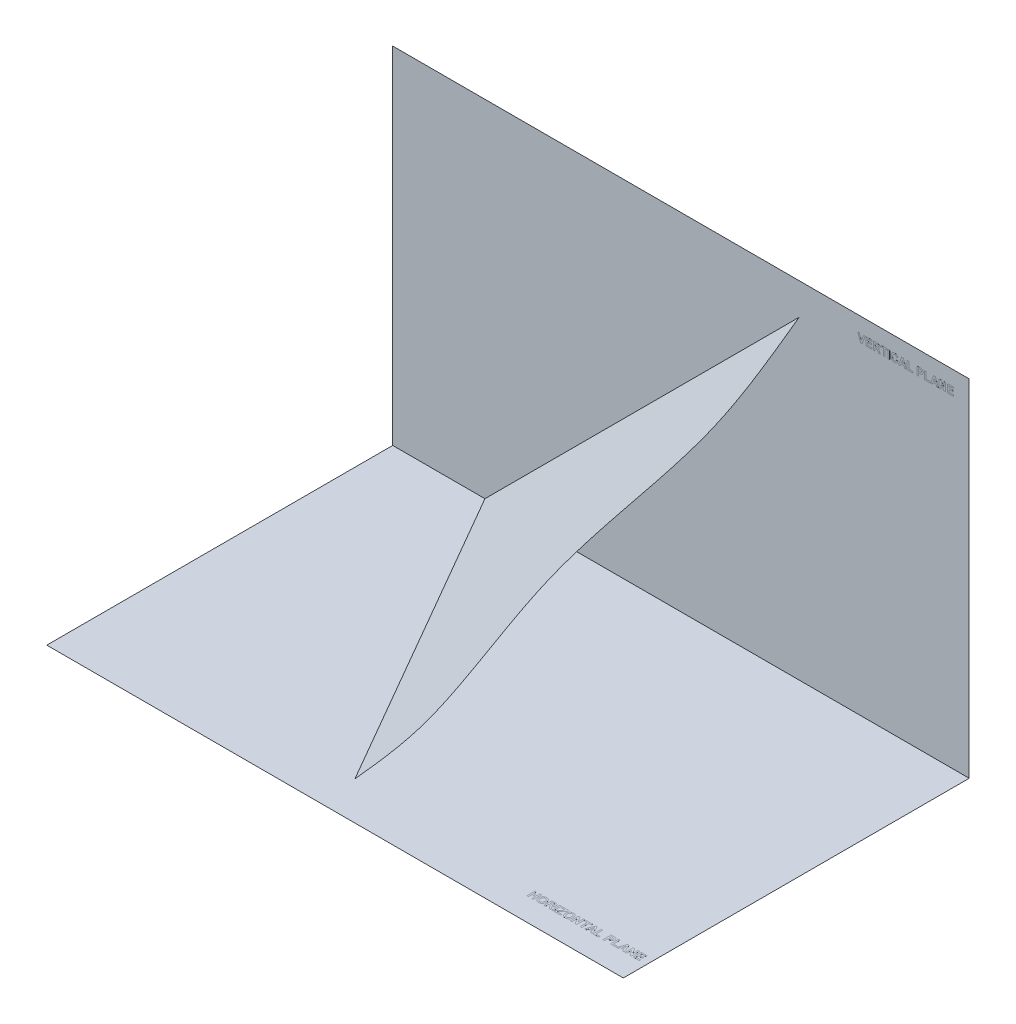
SolidWorks part; units mm, degrees
ref_plane "Front Plane" through (0, 0, 0) normal (0, 0, 1) x (1, 0, 0)
ref_plane "Top Plane" through (0, 0, 0) normal (0, 1, 0) x (1, 0, 0)
ref_plane "Right Plane" through (0, 0, 0) normal (1, 0, 0) x (0, 0, -1)
sketch "Sketch1" plane through (0, 0, 0) normal (0, 0, 1) x (1, 0, 0)
  line L1 (-40, 0) -> (210, 0)
  line L2 (-40, 0) -> (-40, 150)
  line L3 (-40, 150) -> (210, 150)
  line L4 (210, 0) -> (210, 150)
  dimension "D1" = 250
  dimension "D2" = 150
  dimension "D3" = 40
surface "Vertical Plane" sketch "Sketch1"
sketch "Sketch6" plane through (0, 0, 0) normal (0, 0, 1) x (1, 0, 0)
  line L0 (155, 140) -> (210, 140) construction
  line L1 (210, 0) -> (210, 150) construction
  line L2 (210, 150) -> (-40, 150) construction
  text T0 "VERTICAL PLANE" font "Arial" height 3.5
  dimension "D1" = 10
  dimension "D2" = 55
extrude "Vertical  Plane text" add sketch "Sketch6" along normal blind 0.01
sketch "Sketch2" plane through (0, 0, 0) normal (0, 1, 0) x (1, 0, 0)
  line L1 (-40, 0) -> (210, 0)
  line L2 (-40, 0) -> (-40, -150)
  line L3 (-40, -150) -> (210, -150)
  line L4 (210, 0) -> (210, -150)
  dimension "D2" = 150
surface "Horizontal Plane" sketch "Sketch2"
sketch "Sketch7" plane through (0, 0, 0) normal (0, 1, 0) x (1, 0, 0)
  line L0 (155, -140) -> (210, -140) construction
  line L1 (210, -150) -> (210, 0) construction
  line L2 (-40, -150) -> (210, -150) construction
  text T0 "HORIZONTAL PLANE" font "Arial" height 3.5
  dimension "D1" = 10
  dimension "D2" = 55
extrude "Horizontal Plane text" add sketch "Sketch7" along normal blind 0.01
sketch "Vertical Trace" plane through (0, 0, 0) normal (0, 0, 1) x (1, 0, 0)
  line L0 (0, 0) -> (136.2234, 136.2234) construction
  line L1 (210, 0) -> (-40, 0) construction
  dimension "D1" = 45
sketch "Horizontal Trace" plane through (0, 0, 0) normal (0, 1, 0) x (1, 0, 0)
  line L0 (0, 0) -> (77.0291, -133.4183) construction
  line L1 (210, 0) -> (-40, 0) construction
  dimension "D1" = 60
ref_plane "Oblique Plane" through (0, 0, 0) normal (-0.6547, 0.6547, 0.378) x (-0.7559, -0.5669, -0.3273)
sketch "Sketch5" plane through (0, 0, 0) normal (-0.6547, 0.6547, 0.378) x (-0.7559, -0.5669, -0.3273)
  line L0 (-180.2066, -68.1117) -> (0, 0)
  line L1 (0, 0) -> (-101.8999, 115.5436)
  spline S0 degree 3 poles (-180.2066, -68.1117) (-183.8218, -53.3425) (-194.238, -10.7879) (-123.1391, 23.7597) (-141.0806, 92.2491) (-112.8913, 109.0088) (-101.8999, 115.5436) knots 0 0 0 0 0.198717 0.572563 0.833336 1 1 1 1
surface "Section of Oblique Plane" sketch "Sketch5"
sketch "Direction of Horizontal Trace" plane through (0, 0, 0) normal (0, 1, 0) x (1, 0, 0)
  line L0 (0, 0) -> (77.0291, -133.4183) construction
  point P4 (12.5, -21.6506)
  dimension "D1" = 25
ref_plane "Auxiliary Plane" through (12.5, 0, 21.6506) normal (0.5, 0, 0.866) x (0.866, 0, -0.5)
